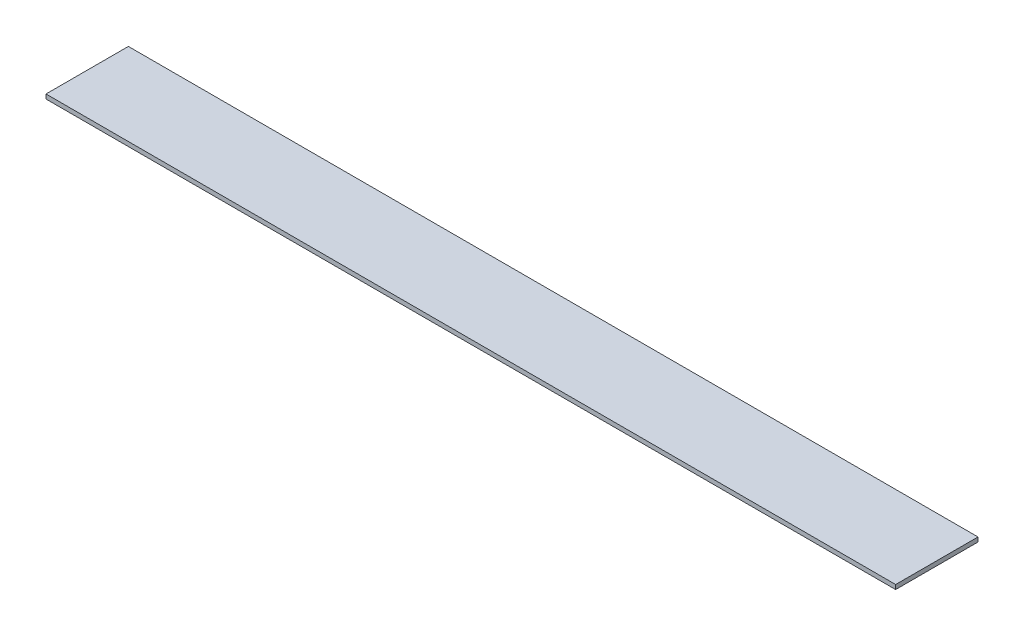
SolidWorks part; units mm, degrees
material "Acrylic (Medium-high impact)"
ref_plane "Front Plane" through (0, 0, 0) normal (0, 0, 1) x (1, 0, 0)
ref_plane "Top Plane" through (0, 0, 0) normal (0, 1, 0) x (1, 0, 0)
ref_plane "Right Plane" through (0, 0, 0) normal (1, 0, 0) x (0, 0, -1)
sketch "Sketch1" plane through (0, 0, 0) normal (0, 1, 0) x (1, 0, 0)
  line L1 (0, 0) -> (612.775, 0)
  line L2 (0, 0) -> (0, 59.4)
  line L3 (0, 59.4) -> (612.775, 59.4)
  line L4 (612.775, 0) -> (612.775, 59.4)
  dimension "D1" = 612.775
  dimension "D2" = 59.4
extrude "Boss-Extrude1" add sketch "Sketch1" along normal blind 3.175 contours L2 L3 L4 L1
